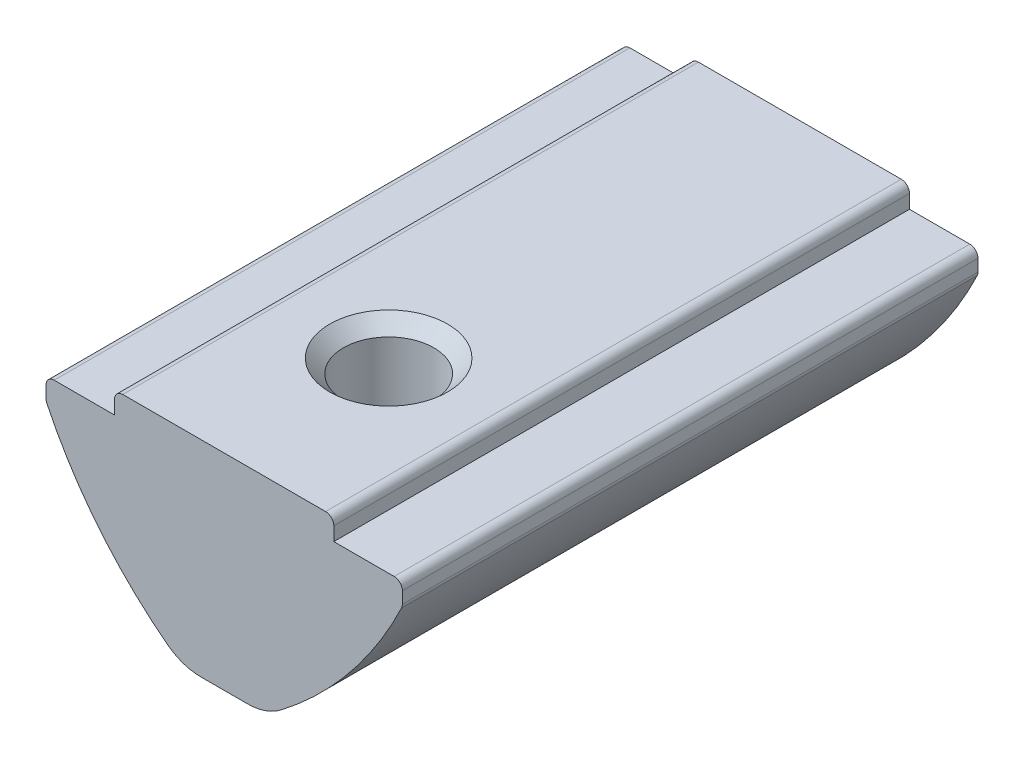
SolidWorks part; units mm, degrees
ref_plane "Спереди" through (0, 0, 0) normal (0, 0, 1) x (1, 0, 0)
ref_plane "Сверху" through (0, 0, 0) normal (0, 1, 0) x (1, 0, 0)
ref_plane "Справа" through (0, 0, 0) normal (1, 0, 0) x (0, 0, -1)
sketch "Эскиз1" plane through (0, 0, 0) normal (0, 0, 1) x (1, 0, 0)
  line L0 (-4, 0) -> (4, 0)
  line L5 (-4, 0) -> (-4, -0.8)
  line L6 (-4, -0.8) -> (-6.5, -0.8)
  line L7 (-6.5, -0.8) -> (-6.5, -1.6)
  line L8 (4, 0) -> (4, -0.8)
  line L9 (4, -0.8) -> (6.5, -0.8)
  line L10 (6.5, -0.8) -> (6.5, -1.6)
  line L11 (-1.5, -7.5) -> (1.5, -7.5)
  arc A0 (-6.5, -1.6) -> (-1.5, -7.5) centre (7.0567, 4.82) ccw
  arc A1 (1.5, -7.5) -> (6.5, -1.6) centre (-7.0567, 4.82) ccw
  point P0 (0, -7.5)
  point P4 (0, 0)
  dimension "D7" = 15
  dimension "D1" = 8
  dimension "D2" = 13
  dimension "D3" = 0.8
  dimension "D4" = 3
  dimension "D5" = 0.8
  dimension "D6" = 7.5
extrude "Бобышка-Вытянуть1" add sketch "Эскиз1" along normal mid plane 21
fillet "Скругление1" radius 0.3 6 edges at (6.5, -1.6, 0) (6.5, -0.8, 0) (-6.5, -0.8, 0) (-6.5, -1.6, 0) (4, 0, 0) (-4, 0, 0)
fillet "Скругление2" radius 2 2 edges at (1.5, -7.5, 0) (-1.5, -7.5, 0)
hole_wizard "Отверстие обработанное метчиком M41" positions "Эскиз2" profile "Эскиз4" tap size "M4" standard "ISO" end condition through all
sketch "Эскиз2" plane through (0, 0, 0) normal (0, 1, 0) x (1, 0, 0)
  line L0 (3.7, -10.5) -> (-3.7, -10.5) construction
  point P0 (0, -4.5)
  dimension "D1" = 6
sketch "Эскиз4" plane through (0, 0, 4.5) normal (1, 0, 0) x (0, 0, 1)
  line L0 (0, 0) -> (0, 7.5)
  line L1 (0, 7.5) -> (1.65, 7.5)
  line L2 (1.65, 7.5) -> (1.65, 0.5)
  line L3 (1.65, 0.5) -> (2.15, 0)
  line L5 (2.15, 0) -> (0, 0)
  line L6 (-1.65, 0.5) -> (-2.15, 0) construction
  line L11 (0, -6.35) -> (0, 107.95) construction
  dimension "Диаметр проходного сверла" = 3.3
  dimension "Глубина проходного сверла" = 7.5
  dimension "Диаметр передней зенковки" = 4.3
  dimension "Угол передней зенковки" = 90
cosmetic thread "Отверстие резьбы1" parameters "D2"=4
sketch "Эскиз5" plane through (0, 0, 0) normal (1, 0, 0) x (0, 0, -1)
  line L1 (6.5, -4.3) -> (6.5, -8.3) construction
  line L2 (10.5, -7.0877) -> (10.5, -1.6618) construction
  line L3 (6.5, -4.3) -> (6.5, -8.3)
  line L5 (10.5, -7.5) -> (-3.0851, -7.5) construction
  arc A0 (6.5, -4.3) -> (6.5, -8.3) centre (6.5, -6.3) ccw
  point P3 (4, -7.4722)
  dimension "D3" = 2
  dimension "D1" = 0.8
  dimension "D2" = 4
revolve "Повернуть1" add sketch "Эскиз5" angle 360 about L1
